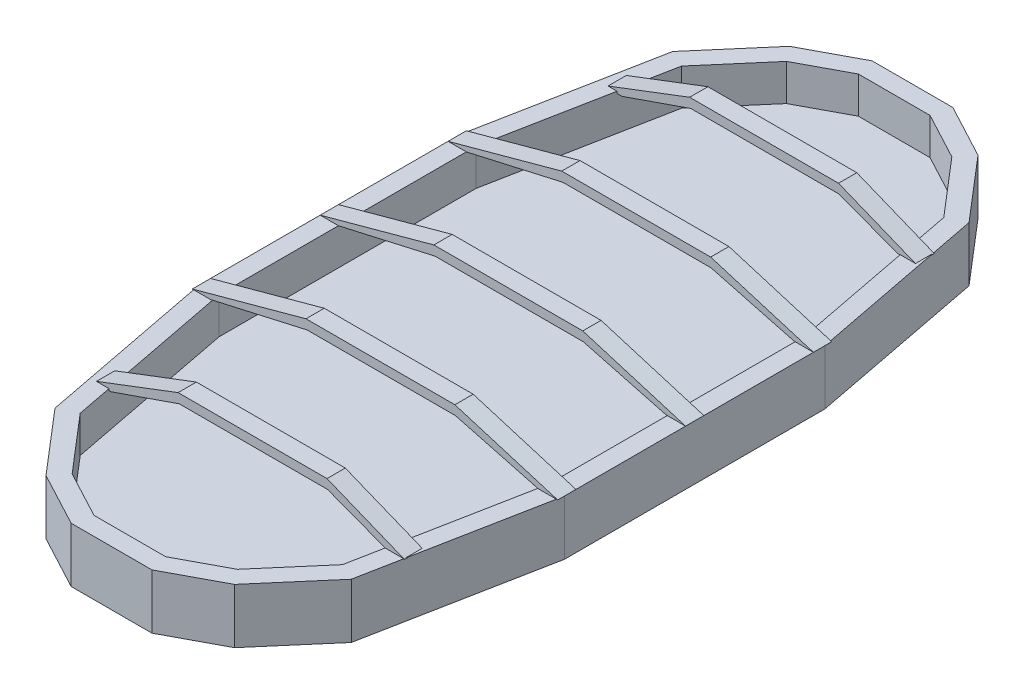
SolidWorks part; units mm, degrees
ref_plane "Front Plane" through (0, 0, 0) normal (0, 0, 1) x (1, 0, 0)
ref_plane "Top Plane" through (0, 0, 0) normal (0, 1, 0) x (1, 0, 0)
ref_plane "Right Plane" through (0, 0, 0) normal (1, 0, 0) x (0, 0, -1)
sketch "Sketch1" plane through (0, 0, 0) normal (0, 1, 0) x (1, 0, 0)
  line L0 (0, -55) -> (0, 55) construction
  line L1 (-100, -71.2628) -> (-100, 71.2628)
  line L2 (100, -71.2628) -> (100, 71.2628)
  line L3 (100, 71.2628) -> (81.0922, 169.0648)
  line L4 (81.0922, 169.0648) -> (51.6041, 203.4676)
  line L5 (51.6041, 203.4676) -> (22.116, 219.1945)
  line L6 (22.116, 219.1945) -> (2.2184, 219.1945)
  line L7 (-100, 71.2628) -> (-81.0922, 169.0648)
  line L8 (-81.0922, 169.0648) -> (-51.6041, 203.4676)
  line L9 (-51.6041, 203.4676) -> (-22.116, 219.1945)
  line L10 (-22.116, 219.1945) -> (-2.2184, 219.1945)
  line L11 (-55, 0) -> (55, 0) construction
  line L12 (100, -71.2628) -> (81.0922, -169.0648)
  line L13 (81.0922, -169.0648) -> (51.6041, -203.4676)
  line L14 (51.6041, -203.4676) -> (22.116, -219.1945)
  line L15 (22.116, -219.1945) -> (2.2184, -219.1945)
  line L16 (-22.116, -219.1945) -> (-2.2184, -219.1945)
  line L17 (-51.6041, -203.4676) -> (-22.116, -219.1945)
  line L18 (-81.0922, -169.0648) -> (-51.6041, -203.4676)
  line L19 (-100, -71.2628) -> (-81.0922, -169.0648)
  line L20 (-2.2184, 219.1945) -> (2.2184, 219.1945)
  line L21 (-2.2184, -219.1945) -> (2.2184, -219.1945)
  point P19 (100, 0)
  point P28 (-100, 0)
  dimension "D1" = 100
  dimension "D2" = 219.1945
extrude "Boss-Extrude1" add sketch "Sketch1" along normal blind 30 contours L3 L4 L5 L6 L20 L10 L9 L8 L7 L1 L19 L18 L17 L16 L21 L15 L14 L13 L12 L2
shell "Shell1" thickness 10
sketch "Sketch2" plane through (0, 0, 0) normal (0, 0, 1) x (1, 0, 0)
  line L0 (43.7304, 46.9926) -> (100, 30)
  line L1 (-37.7643, 47) -> (43.7304, 46.9926)
  line L2 (100, 30) -> (89.3356, 30)
  line L4 (44.0025, 42) -> (89.3356, 30)
  line L9 (-100, 30) -> (-37.7643, 47)
  line L10 (-37.1209, 42) -> (44.0025, 42)
  line L11 (-90, 30) -> (-100, 30)
  line L14 (-37.1209, 42) -> (-90, 30)
  point P13 (-37.7643, 47)
  point P14 (-37.1209, 42)
  point P15 (43.7304, 46.9926)
  point P16 (44.0025, 42)
  dimension "D3" = 10
ref_plane "Plane2" through (0, 0, 70) normal (0, 0, 1) x (1, 0, 0)
ref_plane "Plane3" through (0, 0, -70) normal (0, 0, 1) x (1, 0, 0)
sketch "Sketch4" plane through (0, 0, 70) normal (0, 0, 1) x (1, 0, 0)
  line L0 (-100, 30) -> (-37.7643, 47)
  line L1 (-37.7643, 47) -> (43.7304, 46.9926)
  line L2 (43.7304, 46.9926) -> (100, 30)
  line L3 (100, 30) -> (89.3356, 30)
  line L4 (89.3356, 30) -> (44.0025, 42)
  line L7 (44.0025, 42) -> (-37.1209, 42)
  line L8 (-37.1209, 42) -> (-90, 30)
  line L9 (-90, 30) -> (-100, 30)
sketch "Sketch5" plane through (0, 0, -70) normal (0, 0, 1) x (1, 0, 0)
  line L0 (-100, 30) -> (-37.7643, 47)
  line L1 (-37.7643, 47) -> (43.7304, 46.9926)
  line L2 (43.7304, 46.9926) -> (100, 30)
  line L3 (100, 30) -> (89.3356, 30)
  line L4 (89.3356, 30) -> (44.0025, 42)
  line L5 (44.0025, 42) -> (-37.1209, 42)
  line L6 (-37.1209, 42) -> (-90, 30)
  line L7 (-90, 30) -> (-100, 30)
ref_plane "Plane4" through (0, 0, -140) normal (0, 0, 1) x (1, 0, 0)
sketch "Sketch7" plane through (0, 0, -140) normal (0, 0, 1) x (1, 0, 0)
  line L1 (86.1321, 29.8844) -> (43.7304, 46.9926)
  line L2 (43.7304, 46.9926) -> (-37.7643, 47)
  line L3 (-37.7643, 47) -> (-85.2389, 28.9366)
  line L4 (-85.2389, 28.9366) -> (-74.778, 28.9366)
  line L6 (-37.1209, 42) -> (44.0025, 42)
  line L7 (-37.1209, 42) -> (-74.778, 28.9366)
  line L8 (86.1321, 29.8844) -> (76.0059, 29.8844)
  line L9 (76.0059, 29.8844) -> (44.0025, 42)
  point P13 (0, 0)
  point P15 (76.0059, 29.8844)
ref_plane "Plane5" through (0, 0, 140) normal (0, 0, 1) x (1, 0, 0)
sketch "Sketch8" plane through (0, 0, 140) normal (0, 0, 1) x (1, 0, 0)
  line L0 (-85.2389, 28.9366) -> (-37.7643, 47)
  line L1 (-37.7643, 47) -> (43.7304, 46.9926)
  line L2 (43.7304, 46.9926) -> (86.1321, 29.8844)
  line L3 (86.1321, 29.8844) -> (76.0059, 29.8844)
  line L4 (76.0059, 29.8844) -> (44.0025, 42)
  line L6 (44.0025, 42) -> (-37.1209, 42)
  line L7 (-37.1209, 42) -> (-74.778, 28.9366)
  line L8 (-74.778, 28.9366) -> (-85.2389, 28.9366)
  point P11 (44.0025, 42)
extrude "Boss-Extrude2" add sketch "Sketch8" along normal blind 5 and the other way blind 5 contours L1 L2 L3 L4 L6 L7 L8 L0
extrude "Boss-Extrude3" add sketch "Sketch4" along normal blind 5 and the other way blind 5 contours L7 L8 L9 L0 L1 L2 L3 L4
extrude "Boss-Extrude4" add sketch "Sketch5" along normal blind 5 and the other way blind 5 contours L5 L6 L7 L0 L1 L2 L3 L4
extrude "Boss-Extrude5" add sketch "Sketch7" along normal blind 5 and the other way blind 5 contours L1 L2 L3 L4 L7 L6 L9 L8
extrude "Boss-Extrude6" add sketch "Sketch2" along normal blind 5 and the other way blind 5 contours L1 L0 L2 L4 L10 L14 L11 L9
